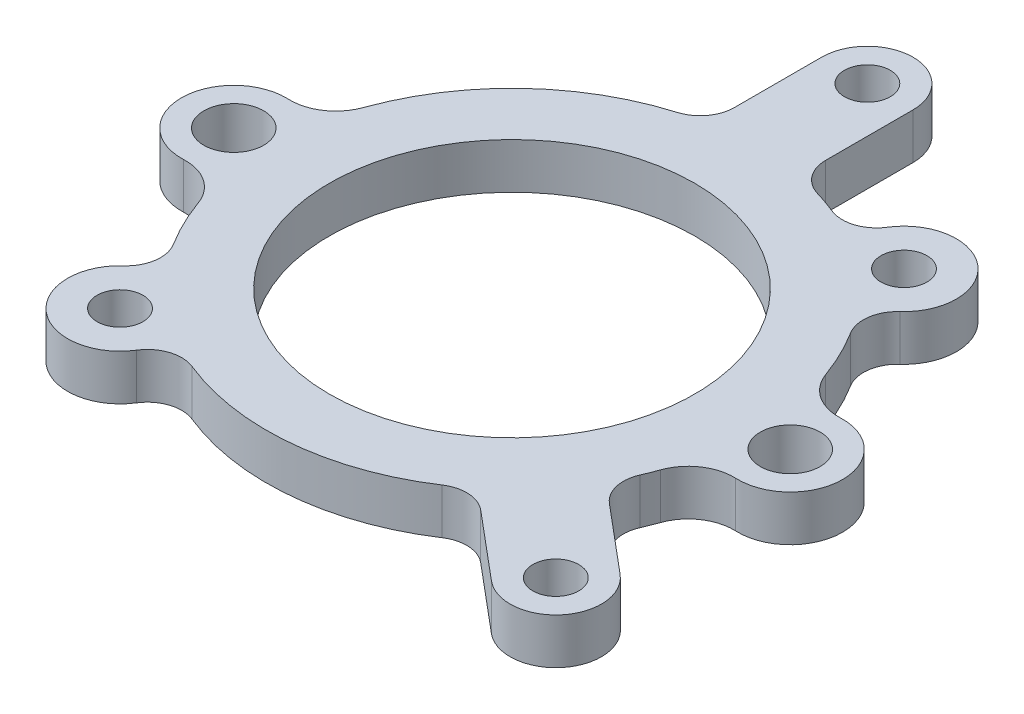
SolidWorks part; units mm, degrees
ref_plane "Front Plane" through (0, 0, 0) normal (0, 0, 1) x (1, 0, 0)
ref_plane "Top Plane" through (0, 0, 0) normal (0, 1, 0) x (1, 0, 0)
ref_plane "Right Plane" through (0, 0, 0) normal (1, 0, 0) x (0, 0, -1)
sketch "Sketch1" plane through (0, 0, 0) normal (0, 1, 0) x (1, 0, 0)
  line L0 (-30.9499, 0) -> (30.9499, 0) construction
  line L1 (19.8942, 23.709) -> (-19.8942, -23.709) construction
  line L2 (0, 0) -> (30.2804, -25.4083) construction
  line L3 (19.5765, -23.0581) -> (27.0151, -29.2998)
  line L4 (26.1072, -15.2751) -> (33.5458, -21.5168)
  line L5 (0, 0) -> (0, 39.5283) construction
  line L6 (27.0151, -29.2998) -> (33.5458, -21.5168) construction
  line L7 (-5.08, 39.5283) -> (-5.08, 29.818)
  line L8 (5.08, 39.5283) -> (5.08, 29.818)
  circle A0 centre (0, 0) radius 20.32
  arc A1 (-25.7134, -9.1861) -> (-23.12, -14.5267) centre (0, 0) ccw
  circle A2 centre (-30.9499, 0) radius 3.3274
  circle A3 centre (30.9499, 0) radius 3.3274
  arc A4 (30.7081, -5.8195) -> (30.7081, 5.8195) centre (30.9499, 0) ccw
  arc A5 (-30.7081, 5.8195) -> (-30.7081, -5.8195) centre (-30.9499, 0) ccw
  arc A6 (25.7134, 9.1861) -> (23.12, 14.5267) centre (0, 0) ccw
  arc A7 (30.7081, -5.8195) -> (25.7134, -9.1861) centre (30.4973, -10.8952) ccw
  arc A8 (30.7081, 5.8195) -> (25.7134, 9.1861) centre (30.4973, 10.8952) cw
  arc A9 (-30.7081, -5.8195) -> (-25.7134, -9.1861) centre (-30.4973, -10.8952) cw
  arc A10 (-30.7081, 5.8195) -> (-25.7134, 9.1861) centre (-30.4973, 10.8952) ccw
  arc A13 (-23.7947, -19.3833) -> (-14.9569, -26.7991) centre (-19.8942, -23.709) ccw
  arc A14 (23.7947, 19.3833) -> (14.9569, 26.7991) centre (19.8942, 23.709) ccw
  arc A15 (-10.2913, -25.2913) -> (15.0303, -22.7959) centre (0, 0) ccw
  arc A16 (10.2913, 25.2913) -> (7.8014, 26.1668) centre (0, 0) ccw
  arc A17 (-23.7947, -19.3833) -> (-23.12, -14.5267) centre (-26.3461, -16.5537) ccw
  arc A18 (-14.9569, -26.7991) -> (-10.2913, -25.2913) centre (-11.7273, -28.8204) cw
  arc A19 (23.7947, 19.3833) -> (23.12, 14.5267) centre (26.3461, 16.5537) ccw
  arc A20 (14.9569, 26.7991) -> (10.2913, 25.2913) centre (11.7273, 28.8204) cw
  arc A21 (27.0151, -29.2998) -> (33.5458, -21.5168) centre (30.2804, -25.4083) ccw
  arc A22 (25.0596, -10.8434) -> (25.7134, -9.1861) centre (0, 0) ccw
  arc A23 (26.1072, -15.2751) -> (25.0596, -10.8434) centre (28.5563, -12.3565) cw
  arc A24 (19.5765, -23.0581) -> (15.0303, -22.7959) centre (17.1275, -25.9768) ccw
  arc A25 (5.08, 39.5283) -> (-5.08, 39.5283) centre (0, 39.5283) ccw
  arc A26 (-7.8014, 26.1668) -> (-25.7134, 9.1861) centre (0, 0) ccw
  arc A27 (5.08, 29.818) -> (7.8014, 26.1668) centre (8.89, 29.818) ccw
  arc A28 (-5.08, 29.818) -> (-7.8014, 26.1668) centre (-8.89, 29.818) cw
  point P8 (0, 0)
  point P16 (26.9716, 4.2542)
  point P23 (0, 0)
  point P34 (-14.0781, -23.396)
  point P39 (14.0781, 23.396)
  point P47 (23.817, -13.3534)
  point P51 (17.2863, -21.1364)
  point P60 (-5.08, 26.8283)
  dimension "D1" = 40.64
  dimension "D2" = 6.985
  dimension "D3" = 61.8998
  dimension "D4" = 6.6548
  dimension "D5" = 2.4972
  dimension "D6" = 5.08
  dimension "D8" = 3.81
  dimension "D13" = 3.81
  dimension "D16" = 3.81
  dimension "D7" = 50
  dimension "D10" = 40
  dimension "D11" = 10.16
  dimension "D12" = 12.7
  dimension "D14" = 10.16
  dimension "D15" = 12.7
extrude "Boss-Extrude1" add sketch "Sketch1" along normal blind 5.08
hole_wizard "1/4-20 Tapped Hole1" positions "3DSketch1" profile "Sketch2" tap size "1/4-20" standard "Ansi Inch" end condition through all
sketch3d "3DSketch1"
  line L0 (0, 5.08, -39.5283) -> (0, 0, -39.5283) construction
  line L1 (19.8942, 5.08, -23.709) -> (19.8942, 0, -23.709) construction
  line L2 (30.2804, 5.08, 25.4083) -> (30.2804, 0, 25.4083) construction
  line L3 (-19.8942, 5.08, 23.709) -> (-19.8942, 0, 23.709) construction
  point P0 (0, 5.08, -39.5283)
  point P4 (19.8942, 5.08, -23.709)
  point P8 (30.2804, 5.08, 25.4083)
  point P12 (-19.8942, 5.08, 23.709)
sketch "Sketch2" plane through (0, 5.08, -39.5283) normal (1, 0, 0) x (0, 0, 1)
  line L0 (0, 0) -> (0, 5.08)
  line L1 (0, 5.08) -> (2.5527, 5.08)
  line L2 (2.5527, 5.08) -> (2.5527, 0)
  line L5 (2.5527, 0) -> (0, 0)
  line L11 (0, -6.35) -> (0, 107.95) construction
  dimension "Thru Tap Drill Dia." = 5.1054
  dimension "Thru Tap Drill Depth" = 5.08
cosmetic thread "Hole Thread1" parameters "D2"=6.35
cosmetic thread "Hole Thread2" parameters "D2"=6.35
cosmetic thread "Hole Thread3" parameters "D2"=6.35
cosmetic thread "Hole Thread4" parameters "D2"=6.35
